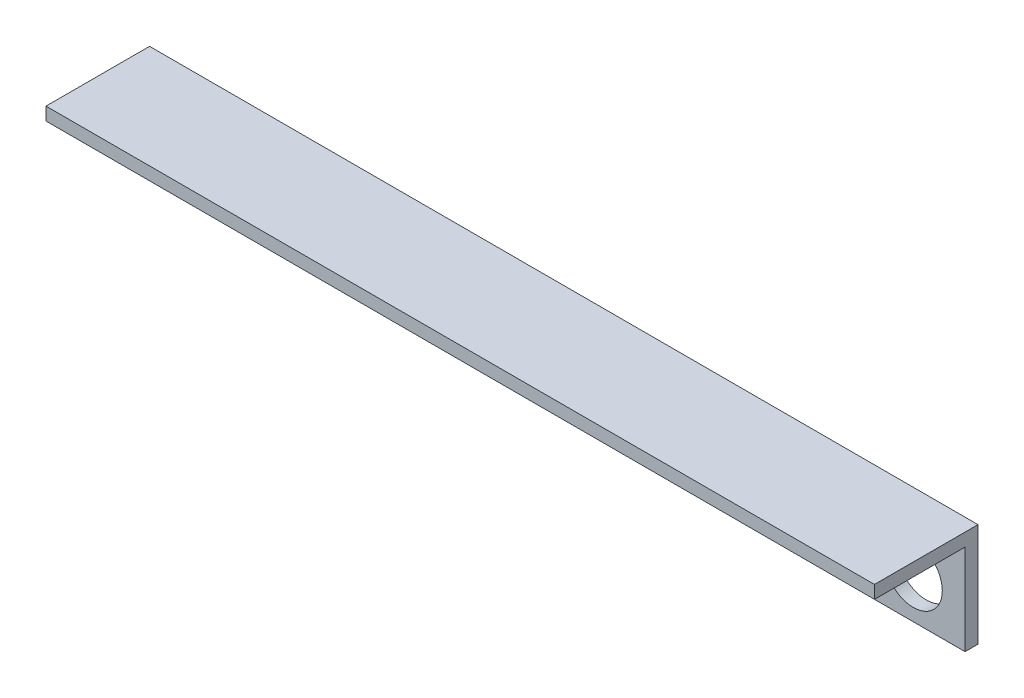
SolidWorks part; units mm, degrees
material "5052-H32"
ref_plane "Front Plane" through (0, 0, 0) normal (0, 0, 1) x (1, 0, 0)
ref_plane "Top Plane" through (0, 0, 0) normal (0, 1, 0) x (1, 0, 0)
ref_plane "Right Plane" through (0, 0, 0) normal (1, 0, 0) x (0, 0, -1)
sketch "Sketch1" plane through (0, 0, 0) normal (1, 0, 0) x (0, 0, -1)
  line L0 (0, 0) -> (0, 12.7)
  line L1 (0, 55) -> (0, -55) construction
  line L11 (0, 12.7) -> (-12.7, 12.7)
  line L13 (-1.5875, 0) -> (-1.5875, 11.1125)
  line L14 (-1.5875, 11.1125) -> (-12.7, 11.1125)
  line L15 (-12.7, 11.1125) -> (-12.7, 12.7)
  line L16 (-1.5875, 0) -> (0, 0)
  dimension "D1" = 1.5875
  dimension "D2" = 12.7
  dimension "D3" = 11.1125
extrude "Boss-Extrude1" add sketch "Sketch1" along normal blind 57.15 and the other way blind 44.45
sketch "Sketch3" plane through (0, 0, 0) normal (0, 0, -1) x (-1, 0, 0)
  line L1 (-57.15, 0) -> (-57.15, 12.7) construction
  line L2 (25.4, 5.08) -> (-50.8, 5.08) construction
  line L3 (44.45, 12.7) -> (-57.15, 12.7) construction
  circle A0 centre (25.4, 5.08) radius 3.556
  circle A1 centre (-50.8, 5.08) radius 3.556
  dimension "D1" = 7.112
  dimension "D2" = 7.62
  dimension "D3" = 76.2
  dimension "D4" = 6.35
extrude "Cut-Extrude1" cut sketch "Sketch3" against normal through all
